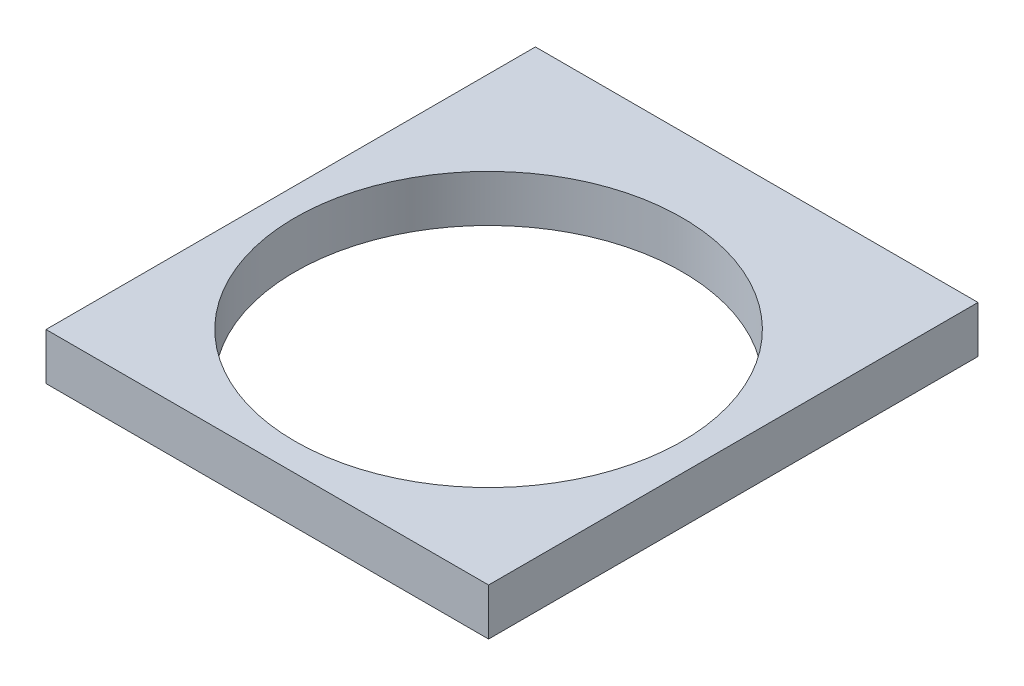
SolidWorks part; units mm, degrees
ref_plane "Front" through (0, 0, 0) normal (0, 0, 1) x (1, 0, 0)
ref_plane "Top" through (0, 0, 0) normal (0, 1, 0) x (1, 0, 0)
ref_plane "Right" through (0, 0, 0) normal (1, 0, 0) x (0, 0, -1)
sketch "Sketch1" plane through (0, 0, 0) normal (0, 1, 0) x (1, 0, 0)
  line L0 (-30, 30) -> (-30, 36.35)
  line L1 (30, -30) -> (-30, -30)
  line L2 (30, -30) -> (30, 30)
  line L4 (-30, -30) -> (-30, 30)
  line L5 (30, -30) -> (-30, 30) construction
  line L6 (30, 30) -> (-30, -30) construction
  line L7 (-30, 36.35) -> (30, 36.35)
  line L8 (30, 36.35) -> (30, 30)
  circle A0 centre (0, 0) radius 26.25
  point P0 (0, 0)
  dimension "D3" = 52.5
  dimension "D1" = 60
  dimension "D2" = 60
  dimension "D4" = 6.35
extrude "Boss-Extrude2" add sketch "Sketch1" along normal blind 6.35
